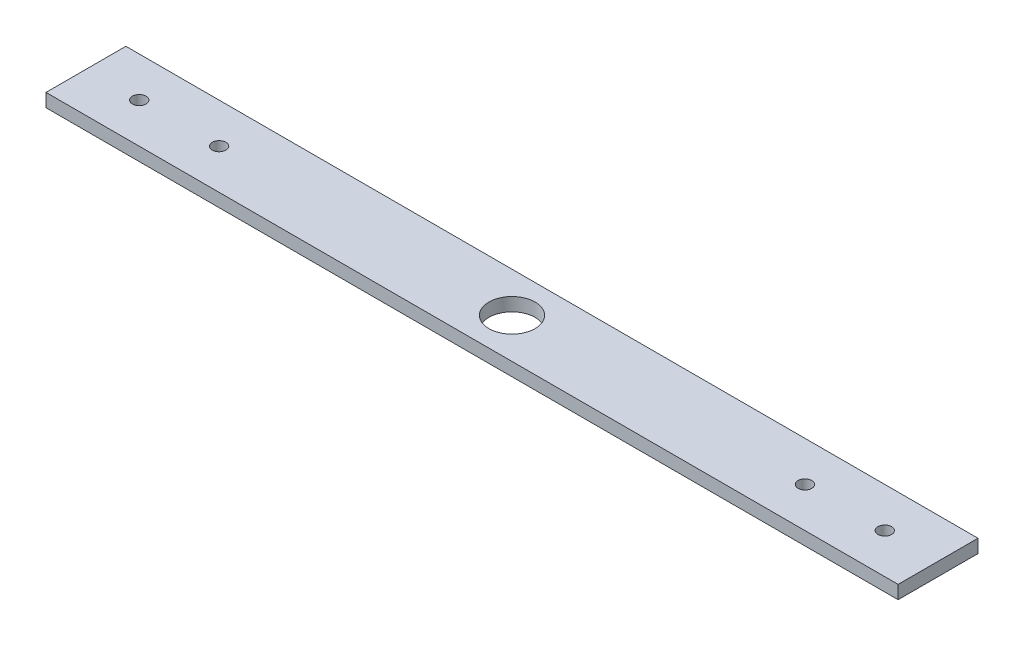
SolidWorks part; units mm, degrees
material "6061-T6 (SS)"
ref_plane "Front Plane" through (0, 0, 0) normal (0, 0, 1) x (1, 0, 0)
ref_plane "Top Plane" through (0, 0, 0) normal (0, 1, 0) x (1, 0, 0)
ref_plane "Right Plane" through (0, 0, 0) normal (1, 0, 0) x (0, 0, -1)
sketch "Sketch1" plane through (0, 0, 0) normal (0, 1, 0) x (1, 0, 0)
  line L1 (-203.2, -19.05) -> (203.2, -19.05)
  line L2 (-203.2, -19.05) -> (-203.2, 19.05)
  line L3 (-203.2, 19.05) -> (203.2, 19.05)
  line L4 (203.2, -19.05) -> (203.2, 19.05)
  line L5 (-203.2, -19.05) -> (203.2, 19.05) construction
  line L6 (-203.2, 19.05) -> (203.2, -19.05) construction
  point P0 (0, 0)
  dimension "D1" = 406.4
  dimension "D2" = 38.1
extrude "Boss-Extrude1" add sketch "Sketch1" along normal blind 6.35
sketch "Sketch2" plane through (0, 6.35, 0) normal (0, 1, 0) x (1, 0, 0)
  circle A0 centre (0, 0) radius 11
  dimension "D1" = 22
extrude "Cut-Extrude1" cut sketch "Sketch2" against normal blind 7.62
hole_wizard "F (0.257) Diameter Hole1" positions "Sketch3" profile "Sketch4" hole size "F" standard "ANSI Inch" end condition through all
sketch "Sketch3" plane through (0, 6.35, 0) normal (0, 1, 0) x (1, 0, 0)
  line L0 (203.2, -19.05) -> (203.2, 19.05) construction
  point P0 (177.8, 0)
  point P2 (139.7, 0)
  dimension "D1" = 25.4
  dimension "D2" = 63.5
sketch "Sketch4" plane through (177.8, 6.35, 0) normal (1, 0, 0) x (0, 0, 1)
  line L0 (0, 0) -> (0, 6.35)
  line L1 (0, 6.35) -> (3.2639, 6.35)
  line L2 (3.2639, 6.35) -> (3.2639, 0)
  line L5 (3.2639, 0) -> (0, 0)
  line L11 (0, -6.35) -> (0, 107.95) construction
  dimension "Thru Hole Dia." = 6.5278
  dimension "Thru Hole Depth" = 6.35
mirror "Mirror1" about plane through (0, 0, 0) normal (1, 0, 0) of "F (0.257) Diameter Hole1"
